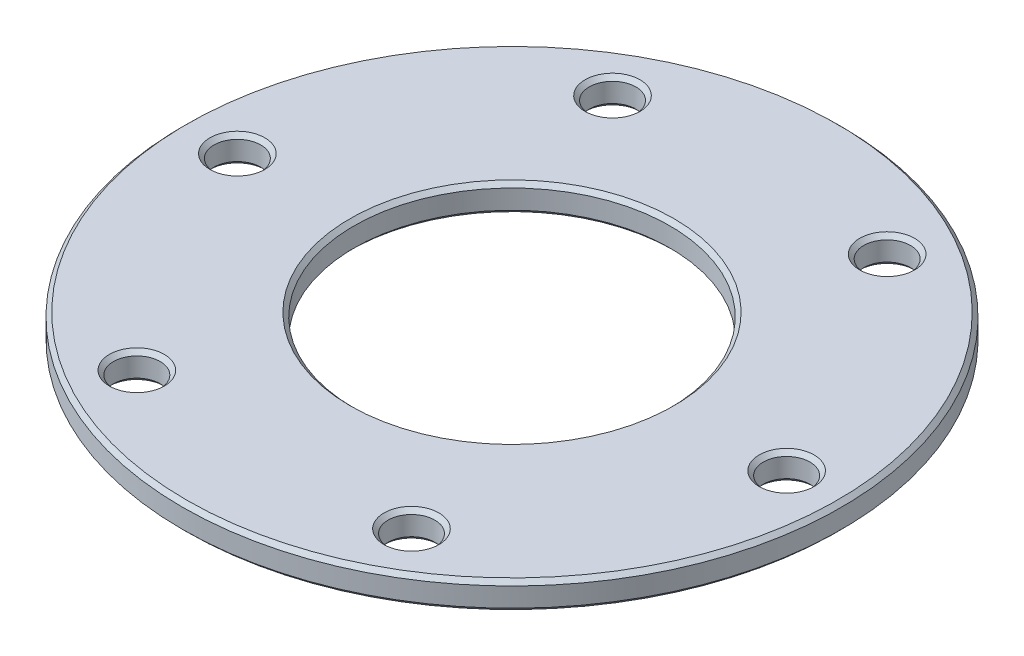
SolidWorks part; units mm, degrees
ref_plane "Front Plane" through (0, 0, 0) normal (0, 0, 1) x (1, 0, 0)
ref_plane "Top Plane" through (0, 0, 0) normal (0, 1, 0) x (1, 0, 0)
ref_plane "Right Plane" through (0, 0, 0) normal (1, 0, 0) x (0, 0, -1)
sketch "Sketch1" plane through (0, 0, 0) normal (0, 1, 0) x (1, 0, 0)
  circle A0 centre (0, 0) radius 24
  circle A1 centre (0, 0) radius 11.5
  dimension "D1" = 23
  dimension "D2" = 48
extrude "Boss-Extrude1" add sketch "Sketch1" along normal blind 2
sketch "Sketch2" plane through (0, 2, 0) normal (0, 1, 0) x (1, 0, 0)
  line L1 (0, 0) -> (-20, 0) construction
  circle A0 centre (-20, 0) radius 1.7
  circle A1 centre (0, 0) radius 20 construction
  circle A2 centre (-10, 17.3205) radius 1.7
  circle A3 centre (10, 17.3205) radius 1.7
  circle A4 centre (20, 0) radius 1.7
  circle A5 centre (10, -17.3205) radius 1.7
  circle A6 centre (-10, -17.3205) radius 1.7
  point P18 (0, 0)
  dimension "D1" = 40
  dimension "D2" = 3.4
  dimension "D3" = 6
extrude "Cut-Extrude1" cut sketch "Sketch2" against normal through all
chamfer "Chamfer2" distance 0.3 angle 45 16 edges at (10, 2, 19.0205) (10, 0, 19.0205) (10, 0, -15.6205) (20, 0, 1.7) (-10, 0, 19.0205) (-20, 0, 1.7) (-10, 0, -15.6205) (-10, 2, -15.6205) (-20, 2, 1.7) (10, 2, -15.6205) (20, 2, 1.7) (-10, 2, 19.0205) (0, 0, 24) (0, 2, 11.5) (0, 2, 24) (0, 0, 11.5)
